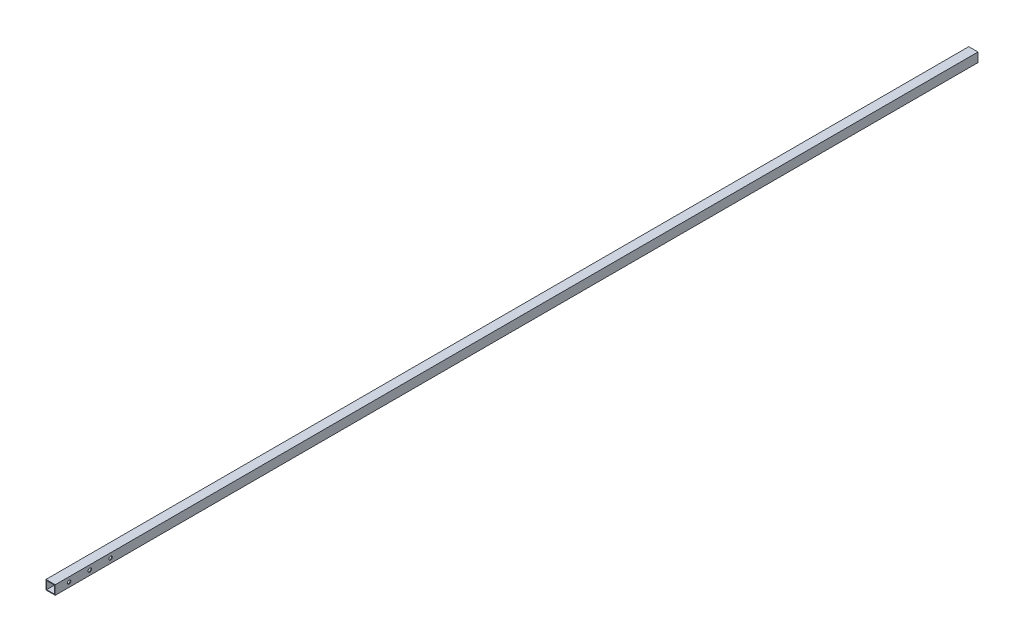
SolidWorks part; units mm, degrees
ref_plane "Alzado" through (0, 0, 0) normal (0, 0, 1) x (1, 0, 0)
ref_plane "Planta" through (0, 0, 0) normal (0, 1, 0) x (1, 0, 0)
ref_plane "Vista lateral" through (0, 0, 0) normal (1, 0, 0) x (0, 0, -1)
sketch "Croquis1" plane through (0, 0, 0) normal (0, 0, 1) x (1, 0, 0)
  line L0 (-17, 17) -> (17, 17)
  line L1 (-20, 20) -> (20, 20)
  line L2 (-20, 20) -> (-20, -20)
  line L3 (-20, -20) -> (20, -20)
  line L4 (20, 20) -> (20, -20)
  line L5 (-20, 20) -> (20, -20) construction
  line L6 (-20, -20) -> (20, 20) construction
  line L7 (17, 17) -> (17, -17)
  line L8 (-17, -17) -> (17, -17)
  line L9 (-17, 17) -> (-17, -17)
  point P0 (0, 0)
  dimension "D1" = 3
extrude "Saliente-Extruir1" add sketch "Croquis1" along normal blind 4000
sketch "Croquis2" plane through (20, 0, 0) normal (1, 0, 0) x (0, 0, -1)
  line L0 (-4000, 0) -> (-3799.7229, 0)
  line L1 (-4000, -20) -> (-4000, 20) construction
  circle A0 centre (-3940, 0) radius 7.5
  circle A1 centre (-3850, 0) radius 7.5
  circle A2 centre (-3760, 0) radius 7.5
  dimension "D1" = 15
  dimension "D2" = 15
  dimension "D3" = 15
  dimension "D4" = 60
  dimension "D5" = 90
  dimension "D6" = 90
extrude "Cortar-Extruir1" cut sketch "Croquis2" against normal blind 40 contours L0 A0 | L0 A0 | L0 A1 | L0 A1 | L0 A2 | L0 A2
